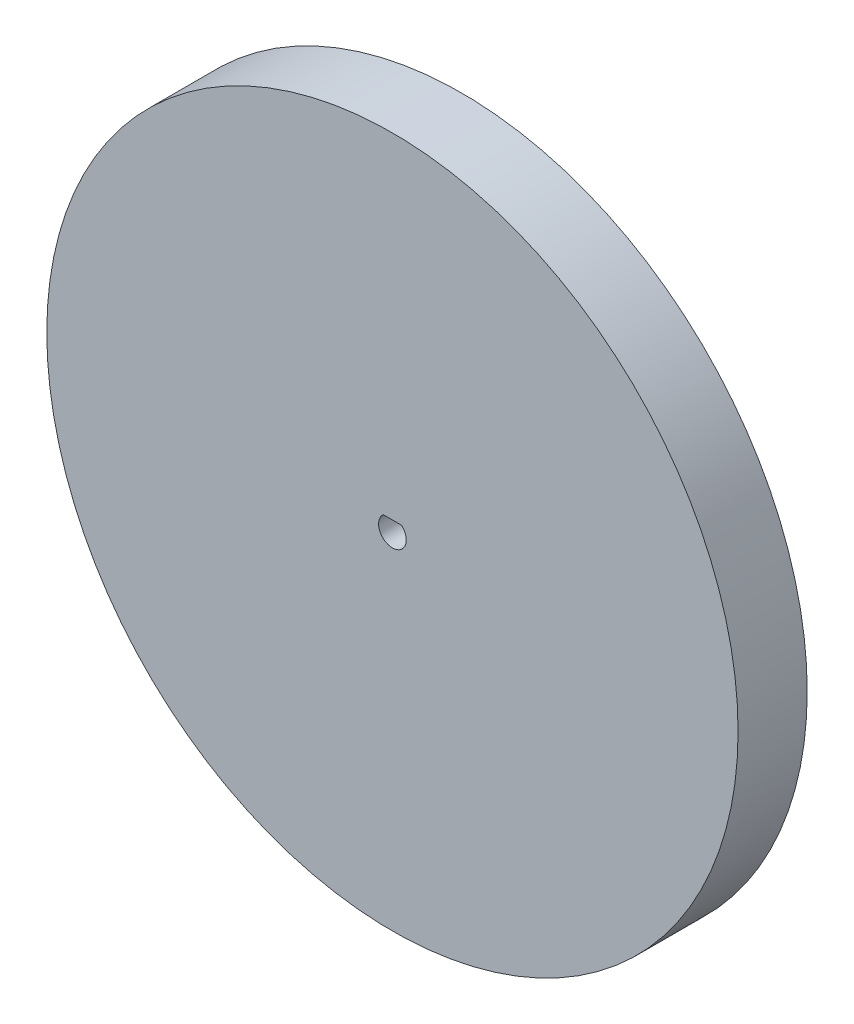
SolidWorks part; units mm, degrees
ref_plane "Front Plane" through (0, 0, 0) normal (0, 0, 1) x (1, 0, 0)
ref_plane "Top Plane" through (0, 0, 0) normal (0, 1, 0) x (1, 0, 0)
ref_plane "Right Plane" through (0, 0, 0) normal (1, 0, 0) x (0, 0, -1)
sketch "Sketch1" plane through (0, 0, 0) normal (0, 0, 1) x (1, 0, 0)
  line L0 (-1.3229, 1.5) -> (1.3229, 1.5)
  circle A0 centre (0, 0) radius 50
  arc A1 (-1.3229, 1.5) -> (1.3229, 1.5) centre (0, 0) ccw
  dimension "D1" = 100
  dimension "D2" = 4
  dimension "D3" = 1.5
extrude "Boss-Extrude1" add sketch "Sketch1" along normal blind 10
